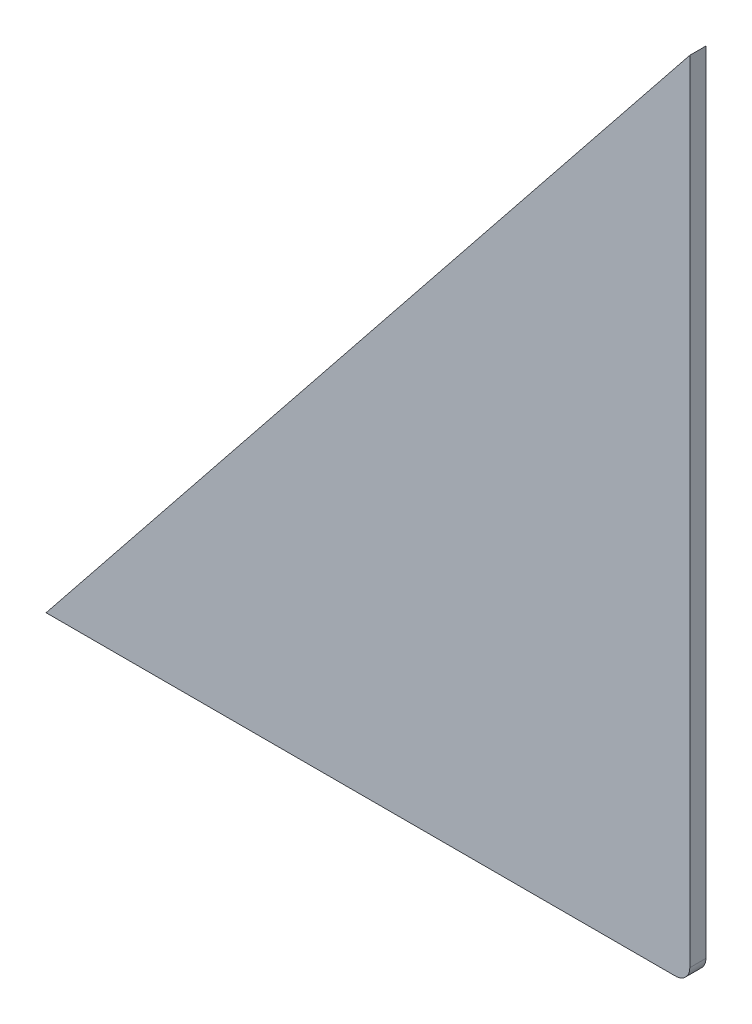
SolidWorks part; units mm, degrees
ref_plane "Front Plane" through (0, 0, 0) normal (0, 0, 1) x (1, 0, 0)
ref_plane "Top Plane" through (0, 0, 0) normal (0, 1, 0) x (1, 0, 0)
ref_plane "Right Plane" through (0, 0, 0) normal (1, 0, 0) x (0, 0, -1)
sketch "Sketch1" plane through (0, 0, 0) normal (0, 0, 1) x (1, 0, 0)
  line L0 (-80, 0) -> (-1.8, 0)
  line L1 (0, 1.8) -> (0, 100)
  line L2 (0, 100) -> (-80, 0)
  arc A0 (-1.8, 0) -> (0, 1.8) centre (-1.8, 1.8) ccw
  point P6 (0, 0)
  dimension "D3" = 1.8
  dimension "D1" = 100
  dimension "D2" = 80
extrude "Boss-Extrude1" add sketch "Sketch1" along normal mid plane 2
